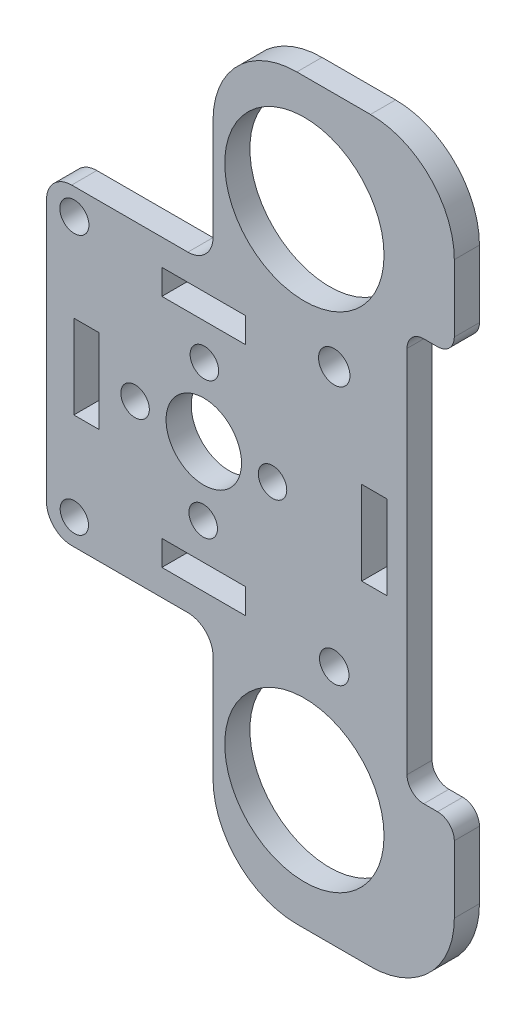
SolidWorks part; units mm, degrees
ref_plane "Front Plane" through (0, 0, 0) normal (0, 0, 1) x (1, 0, 0)
ref_plane "Top Plane" through (0, 0, 0) normal (0, 1, 0) x (1, 0, 0)
ref_plane "Right Plane" through (0, 0, 0) normal (1, 0, 0) x (0, 0, -1)
sketch "Sketch1" plane through (0, 0, 0) normal (0, 0, 1) x (1, 0, 0)
  line L0 (147.062, -92.9701) -> (147.062, -71.8565)
  line L1 (147.062, -92.9701) -> (127.2038, -92.9701)
  line L2 (127.2038, -92.9701) -> (127.2038, -111.5917)
  line L4 (147.062, -151.8871) -> (147.062, -155.8871)
  line L5 (145.9607, -111.5917) -> (157.9607, -111.5917) construction
  line L6 (157.9607, -111.5917) -> (157.9607, -81.5917) construction
  line L7 (157.9607, -111.5917) -> (157.9607, -141.5917) construction
  line L8 (147.062, -71.8565) -> (147.062, -67.8565)
  line L9 (127.2038, -111.5917) -> (127.2038, -130.2155)
  line L10 (127.2038, -130.2155) -> (147.062, -130.2155)
  line L11 (147.062, -130.2155) -> (147.062, -151.8871)
  line L13 (147.062, -67.8565) -> (175.8433, -67.8565)
  line L14 (147.062, -155.8871) -> (175.8433, -155.8871)
  line L15 (175.8433, -67.8565) -> (175.8433, -87.8565)
  line L16 (175.8433, -155.8871) -> (175.8433, -135.8871)
  line L17 (175.8433, -87.8565) -> (170.1989, -87.8565)
  line L18 (175.8433, -135.8871) -> (170.1989, -135.8871)
  line L19 (170.1989, -87.8565) -> (170.1989, -135.8871)
  line L20 (145.9607, -111.5917) -> (131.9607, -111.5917) construction
  line L21 (145.9607, -111.5917) -> (145.9607, -97.5917) construction
  line L22 (145.9607, -111.5917) -> (145.9607, -125.5917) construction
  line L23 (157.9607, -111.5917) -> (166.2936, -111.5917) construction
  line L24 (130.4607, -106.5917) -> (133.4607, -106.5917)
  line L25 (130.4607, -106.5917) -> (130.4607, -116.5917)
  line L26 (130.4607, -116.5917) -> (133.4607, -116.5917)
  line L27 (133.4607, -106.5917) -> (133.4607, -116.5917)
  line L28 (130.4607, -106.5917) -> (133.4607, -116.5917) construction
  line L29 (130.4607, -116.5917) -> (133.4607, -106.5917) construction
  line L30 (140.9607, -99.0917) -> (150.9607, -99.0917)
  line L31 (140.9607, -99.0917) -> (140.9607, -96.0917)
  line L32 (140.9607, -96.0917) -> (150.9607, -96.0917)
  line L33 (150.9607, -99.0917) -> (150.9607, -96.0917)
  line L34 (140.9607, -99.0917) -> (150.9607, -96.0917) construction
  line L35 (140.9607, -96.0917) -> (150.9607, -99.0917) construction
  line L36 (140.9607, -127.0917) -> (150.9607, -127.0917)
  line L37 (140.9607, -127.0917) -> (140.9607, -124.0917)
  line L38 (140.9607, -124.0917) -> (150.9607, -124.0917)
  line L39 (150.9607, -127.0917) -> (150.9607, -124.0917)
  line L40 (140.9607, -127.0917) -> (150.9607, -124.0917) construction
  line L41 (140.9607, -124.0917) -> (150.9607, -127.0917) construction
  line L43 (164.7936, -106.5917) -> (167.7936, -106.5917)
  line L44 (164.7936, -106.5917) -> (164.7936, -116.5917)
  line L45 (164.7936, -116.5917) -> (167.7936, -116.5917)
  line L46 (167.7936, -106.5917) -> (167.7936, -116.5917)
  line L47 (164.7936, -106.5917) -> (167.7936, -116.5917) construction
  line L48 (164.7936, -116.5917) -> (167.7936, -106.5917) construction
  circle A0 centre (130.52, -96.082) radius 1.7379
  circle A2 centre (161.52, -96.082) radius 1.8732
  circle A3 centre (130.52, -127.1142) radius 1.6901
  circle A4 centre (161.52, -127.082) radius 1.7542
  circle A5 centre (154.1576, -111.6623) radius 1.7
  circle A6 centre (145.8901, -119.7886) radius 1.7
  circle A7 centre (137.7638, -111.5212) radius 1.7
  circle A8 centre (146.0313, -103.3948) radius 1.7
  circle A10 centre (145.9607, -111.5917) radius 4.5
  circle A15 centre (157.9607, -81.5917) radius 9.5
  circle A16 centre (157.9607, -141.5917) radius 9.5
  point P2 (0, 0)
  point P44 (145.9607, -111.5917)
  point P47 (106.5258, -71.8662)
  dimension "D1" = 4
  dimension "D4" = 12
  dimension "D5" = 4
  dimension "D10" = 4
  dimension "D2" = 30
  dimension "D3" = 30
  dimension "D6" = 20
  dimension "D7" = 20
  dimension "D11" = 14
  dimension "D12" = 14
  dimension "D13" = 14
  dimension "D14" = 3
  dimension "D15" = 3
  dimension "D16" = 3
  dimension "D17" = 10
  dimension "D18" = 10
  dimension "D19" = 10
  dimension "D20" = 3
  dimension "D21" = 10
extrude "Boss-Extrude1" add sketch "Sketch1" along normal blind 3
fillet "Fillet1" radius 10 4 edges at (175.8433, -155.8871, 1.5) (147.062, -155.8871, 1.5) (147.062, -67.8565, 1.5) (175.8433, -67.8565, 1.5)
fillet "Fillet2" radius 3 4 edges at (147.062, -92.9701, 1.5) (127.2038, -92.9701, 1.5) (127.2038, -130.2155, 1.5) (147.062, -130.2155, 1.5)
fillet "Fillet3" radius 2 4 edges at (170.1989, -87.8565, 1.5) (175.8433, -87.8565, 1.5) (175.8433, -135.8871, 1.5) (170.1989, -135.8871, 1.5)
